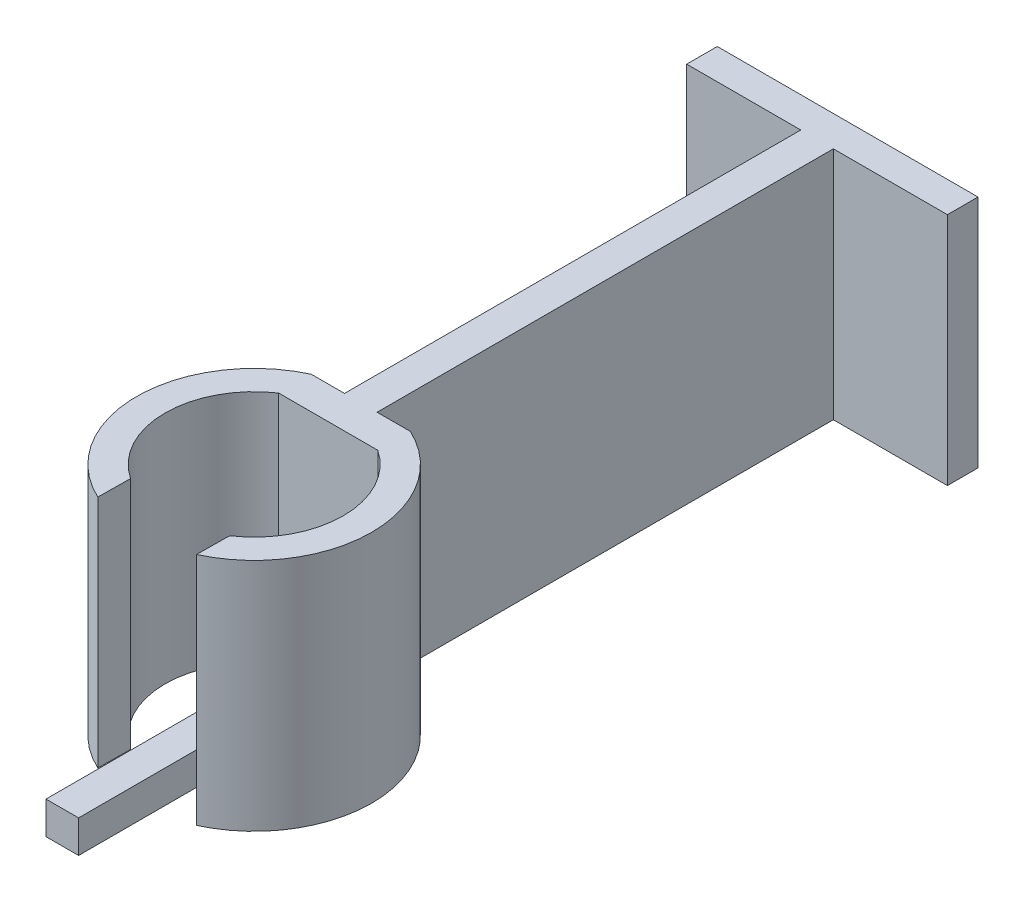
SolidWorks part; units mm, degrees
ref_plane "Front Plane" through (0, 0, 0) normal (0, 0, 1) x (1, 0, 0)
ref_plane "Top Plane" through (0, 0, 0) normal (0, 1, 0) x (1, 0, 0)
ref_plane "Right Plane" through (0, 0, 0) normal (1, 0, 0) x (0, 0, -1)
sketch "Sketch1" plane through (0, 0, 0) normal (0, 1, 0) x (1, 0, 0)
  line L0 (9.652, 10.9674) -> (9.6184, 7.7769)
  line L1 (0, 28.575) -> (9.652, 28.575)
  line L2 (0, 28.575) -> (0, 25.4)
  line L3 (0, 25.4) -> (9.652, 25.4)
  line L4 (9.652, 28.575) -> (9.652, 25.4)
  line L5 (0, 10.9674) -> (-0.034, 7.8083)
  line L7 (3.2385, 73.025) -> (6.4135, 73.025)
  line L8 (3.2385, 73.025) -> (3.2385, 28.575)
  line L9 (3.2385, 28.575) -> (6.4135, 28.575)
  line L10 (6.4135, 73.025) -> (6.4135, 28.575)
  line L11 (17.526, 73.025) -> (-7.874, 73.025)
  line L12 (17.526, 73.025) -> (17.526, 76.0046)
  line L13 (17.526, 76.0046) -> (-7.874, 76.0046)
  line L14 (-7.874, 73.025) -> (-7.874, 76.0046)
  arc A0 (9.652, 10.9674) -> (9.652, 25.4) centre (4.826, 18.1837) ccw
  arc A1 (9.652, 28.575) -> (9.6184, 7.7769) centre (4.826, 18.1837) cw
  arc A2 (0, 10.9674) -> (0, 25.4) centre (4.826, 18.1837) cw
  arc A3 (0, 28.575) -> (-0.034, 7.8083) centre (4.826, 18.1837) ccw
extrude "Boss-Extrude1" add sketch "Sketch1" along normal blind 22.86 contours L2 A3 L5 A2 | L4 L1 L2 L3 | A1 L4 A0 L0 | L14 L11 L7 L12 L13
sketch "Sketch2" plane through (0, 0, 0) normal (0, 0, 1) x (1, 0, 0)
  line L1 (3.2385, 3.175) -> (6.4135, 3.175)
  line L2 (3.2385, 3.175) -> (3.2385, 0)
  line L3 (3.2385, 0) -> (6.4135, 0)
  line L4 (6.4135, 3.175) -> (6.4135, 0)
extrude "Boss-Extrude2" add sketch "Sketch2" along normal blind 0.508 and the other way blind 26.3995 separate body
